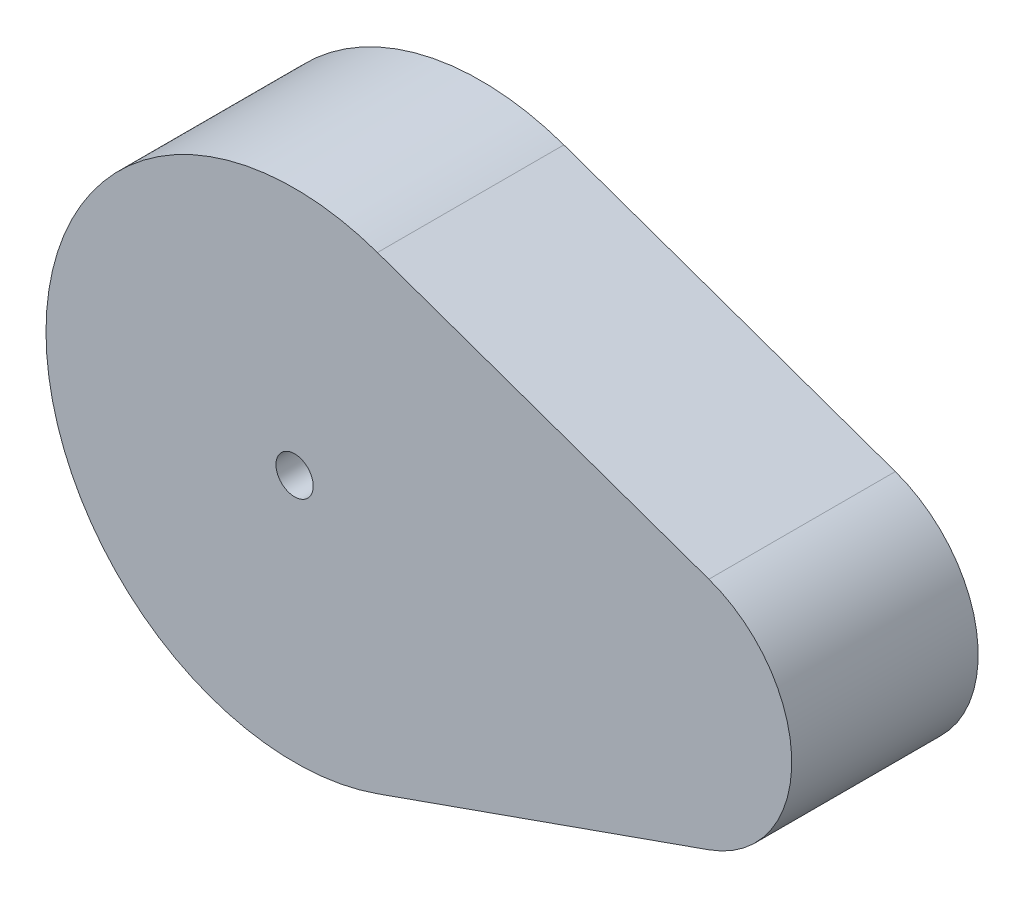
SolidWorks part; units mm, degrees
ref_plane "Front Plane" through (0, 0, 0) normal (0, 0, 1) x (1, 0, 0)
ref_plane "Top Plane" through (0, 0, 0) normal (0, 1, 0) x (1, 0, 0)
ref_plane "Right Plane" through (0, 0, 0) normal (1, 0, 0) x (0, 0, -1)
sketch "Sketch2" plane through (0, 0, 0) normal (0, 1, 0) x (1, 0, 0)
  line L0 (0, 0) -> (0, 6) construction
  dimension "D1" = 6
sketch "Sketch1" plane through (0, 0, 0) normal (0, 0, 1) x (1, 0, 0)
  line L0 (12, 0) -> (0, 0) construction
  line L5 (2.6667, 7.5425) -> (13.3333, 3.7712)
  line L6 (13.3333, -3.7712) -> (2.6667, -7.5425)
  circle A0 centre (0, 0) radius 0.6
  arc A1 (13.3333, 3.7712) -> (13.3333, -3.7712) centre (12, 0) cw
  arc A2 (2.6667, 7.5425) -> (2.6667, -7.5425) centre (0, 0) ccw
  point P10 (16, 0)
  dimension "D1" = 1.2
  dimension "D2" = 8
  dimension "D3" = 4
  dimension "D4" = 16
extrude "Boss-Extrude1" add sketch "Sketch1" against normal up to vertex (6 mm away) up to point (0, 0, -6)
equation "\"t_wood\"= 6' Thickness of the wood"
equation "\"t_glass\"= 2.5'Thickness of glass panels"
equation "\"w_glass\"= 248"
equation "\"h_glass\"= 167"
equation "\"h_food_internal\" = 60"
equation "\"entry_height\"= 20"
equation "\"entry diameter\"= 8"
equation "\"glass_bottom_overlap\"= 8"
equation "\"default_finger_size\"= 12"
equation "\"brood_depth\"= 42"
equation "\"outer_box_depth\" = \"brood_depth\" + ( 2 * \"t_glass\" ) + ( 2 * \"t_wood\" )"
equation "\"outer_box_width\"= \"w_glass\" + ( 2 * \"t_wood\" )"
equation "\"food_top_clearance\"= 10"
equation "\"outer_box_height\"= \"t_wood\" + \"h_glass\" + \"t_wood\" + \"h_food_internal\" + \"food_top_clearance\" + \"t_wood\""
equation "\"food_internal_depth\"= \"brood_depth\" + \"t_glass\" + \"t_glass\" - \"t_wood\" - \"t_wood\""
equation "\"food_channel_clearance_width\"= 14"
equation "\"bar_top_play\"= 4.5"
equation "\"bar_entry_angle\"= 10"
equation "\"bar_width\"= 20"
equation "\"entry_disk_play\"= 0.3"
equation "\"D1@Sketch2\"=\"t_wood\""
